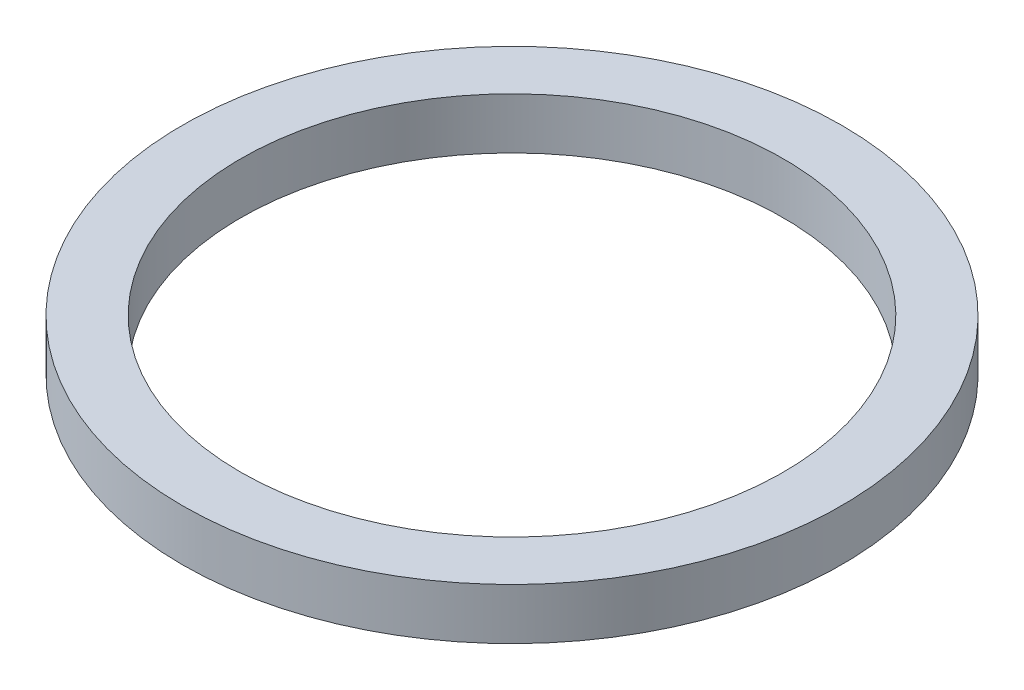
SolidWorks part; units mm, degrees
material "Pine"
ref_plane "Front Plane" through (0, 0, 0) normal (0, 0, 1) x (1, 0, 0)
ref_plane "Top Plane" through (0, 0, 0) normal (0, 1, 0) x (1, 0, 0)
ref_plane "Right Plane" through (0, 0, 0) normal (1, 0, 0) x (0, 0, -1)
sketch "Sketch1" plane through (0, 0, 0) normal (0, 1, 0) x (1, 0, 0)
  line L0 (0, 0) -> (-10.5271, -16.1822) construction
  circle A0 centre (0, 0) radius 15.9
  circle A1 centre (0, 0) radius 19.305
  dimension "D1" = 31.8
  dimension "D2" = 38.61
  dimension "D3" = 19.305
extrude "Boss-Extrude1" add sketch "Sketch1" along normal blind 3 contours A1
